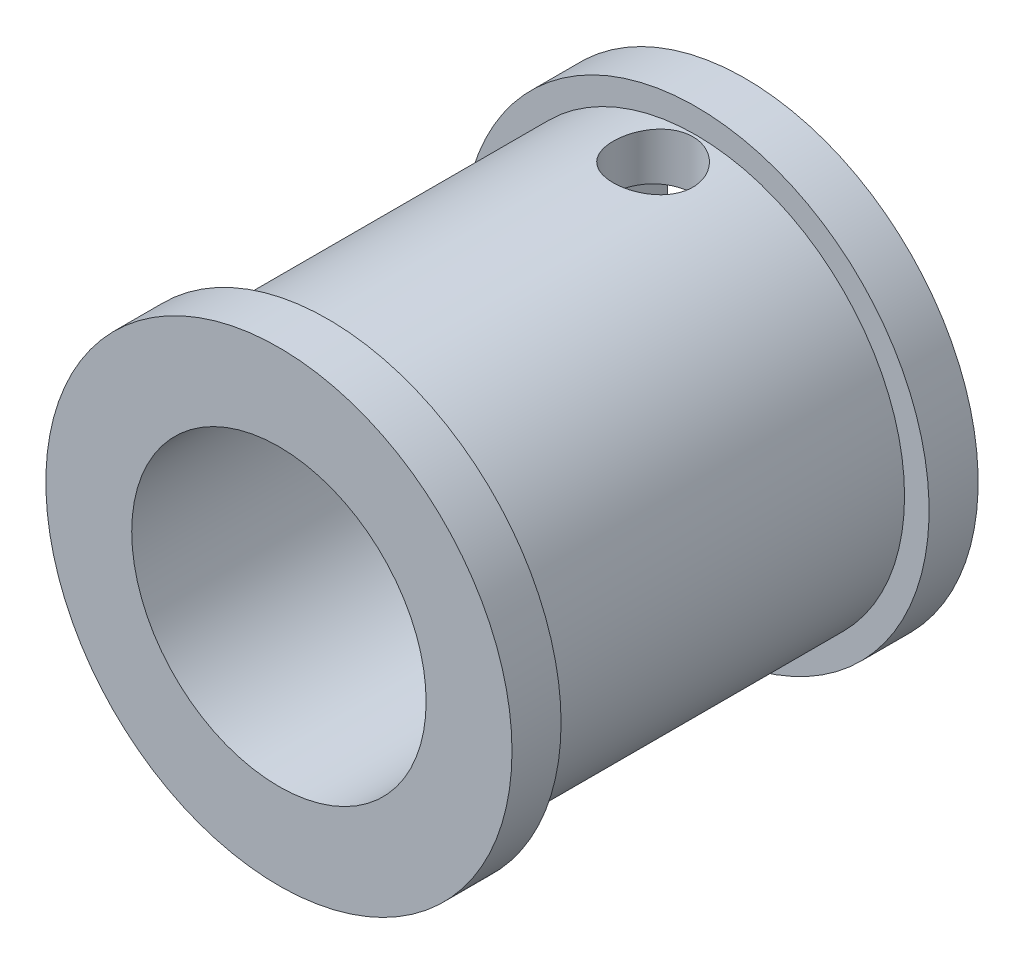
SolidWorks part; units mm, degrees
ref_plane "Alzado" through (0, 0, 0) normal (0, 0, 1) x (1, 0, 0)
ref_plane "Planta" through (0, 0, 0) normal (0, 1, 0) x (1, 0, 0)
ref_plane "Vista lateral" through (0, 0, 0) normal (1, 0, 0) x (0, 0, -1)
sketch "Croquis1" plane through (0, 0, 0) normal (0, 0, 1) x (1, 0, 0)
  circle A1 centre (0, 0) radius 8.5
  dimension "D1" = 17
extrude "Saliente-Extruir1" add sketch "Croquis1" along normal blind 19
sketch "Croquis2" plane through (0, 0, 0) normal (0, 0, -1) x (-1, 0, 0)
  circle A0 centre (0, 0) radius 1.625
  circle A1 centre (0, 0) radius 8.5 construction
  dimension "D1" = 3.25
extrude "Cortar-Extruir1" cut sketch "Croquis2" against normal through all and the other way through all
sketch "Croquis3" plane through (0, 0, 0) normal (0, 0, -1) x (-1, 0, 0)
  line L0 (0, 0) -> (0, 3.5) construction
  line L1 (0, 3.5) -> (-3.17, 3.5) construction
  line L3 (-3.17, 3.5) -> (3.17, 3.5)
  line L4 (-3.17, 3.5) -> (-3.17, 6.5)
  line L5 (-3.17, 6.5) -> (3.17, 6.5)
  line L6 (3.17, 3.5) -> (3.17, 6.5)
  circle A0 centre (0, 0) radius 1.625 construction
  dimension "D1" = 3.17
  dimension "D2" = 3.5
  dimension "D3" = 6.5
extrude "Cortar-Extruir2" cut sketch "Croquis3" against normal blind 7.5
sketch "Croquis4" plane through (0, 0, 0) normal (0, 0, -1) x (-1, 0, 0)
  line L0 (3.17, 3.5) -> (3.17, 6.5) construction
  line L1 (3.17, 6.5) -> (-3.17, 6.5) construction
  circle A0 centre (0, 0) radius 9.5
  circle A2 centre (0, 0) radius 8.5
  dimension "D1" = 17
  dimension "D2" = 19
  dimension "D3" = 3.17
  dimension "D4" = 6.5
extrude "Saliente-Extruir2" add sketch "Croquis4" against normal blind 2
sketch "Croquis5" plane through (0, 0, 19) normal (0, 0, 1) x (1, 0, 0)
  circle A1 centre (0, 0) radius 9.5
  circle A3 centre (0, 0) radius 1.625 construction
  circle A5 centre (0, 0) radius 8.5
  dimension "D1" = 17
  dimension "D2" = 19
extrude "Saliente-Extruir3" add sketch "Croquis5" against normal blind 2
sketch "Croquis7" plane through (0, 6.5, 0) normal (0, -1, 0) x (1, 0, 0)
  line L0 (-3.17, 7.5) -> (3.17, 0) construction
  circle A0 centre (0, 3.75) radius 1.625
extrude "Cortar-Extruir4" cut sketch "Croquis7" against normal blind 3 and the other way blind 6.7
sketch "Croquis9" plane through (0, 0, 19) normal (0, 0, 1) x (1, 0, 0)
  circle A0 centre (0, 0) radius 6
  circle A1 centre (0, 0) radius 1.625 construction
  dimension "D1" = 12
extrude "Cortar-Extruir5" cut sketch "Croquis9" against normal blind 9
